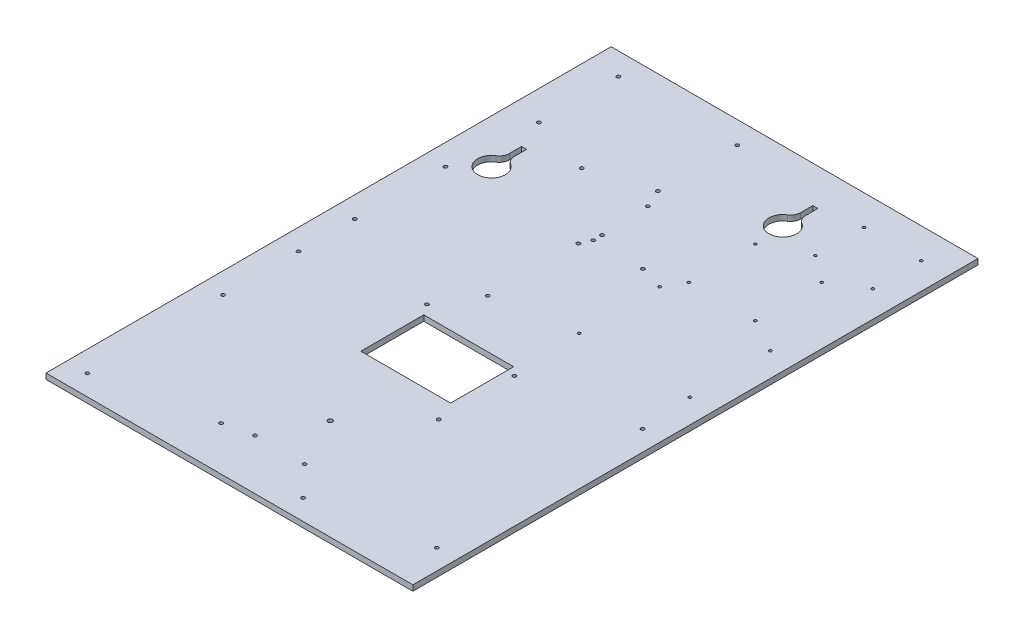
SolidWorks part; units mm, degrees
material "Acrylic (Medium-high impact)"
ref_plane "Front Plane" through (0, 0, 0) normal (0, 0, 1) x (1, 0, 0)
ref_plane "Top Plane" through (0, 0, 0) normal (0, 1, 0) x (1, 0, 0)
ref_plane "Right Plane" through (0, 0, 0) normal (1, 0, 0) x (0, 0, -1)
sketch "Sketch1" plane through (0, 0, 0) normal (0, 1, 0) x (1, 0, 0)
  line L0 (-836.7628, 790.2433) -> (-836.7628, 232.9433)
  line L1 (-836.7628, 790.2433) -> (-836.7628, 796.5933)
  line L2 (-836.7628, 796.5933) -> (-466.7628, 796.5933)
  line L3 (-466.7628, 796.5933) -> (-466.7628, 790.2433)
  line L4 (-836.7628, 232.9433) -> (-836.7628, 226.5933)
  line L5 (-836.7628, 226.5933) -> (-466.7628, 226.5933)
  line L6 (-466.7628, 226.5933) -> (-466.7628, 232.9433)
  line L7 (-466.7628, 790.2433) -> (-836.7628, 790.2433) construction
  line L8 (-466.7628, 232.9433) -> (-466.7628, 790.2433)
  line L9 (-836.7628, 232.9433) -> (-466.7628, 232.9433) construction
  circle A0 centre (-807.0628, 774.0873) radius 1.778
  circle A1 centre (-807.0628, 694.0873) radius 1.778
  circle A2 centre (-687.0628, 694.0873) radius 1.778
  circle A3 centre (-687.0628, 774.0873) radius 1.778
  circle A4 centre (-551.4378, 766.1683) radius 1.397
  circle A5 centre (-551.4378, 717.1683) radius 1.397
  circle A6 centre (-493.4378, 717.1683) radius 1.397
  circle A7 centre (-493.4378, 766.1683) radius 1.397
  circle A8 centre (-591.7378, 696.9683) radius 1.397
  circle A9 centre (-591.7378, 629.9683) radius 1.397
  circle A10 centre (-524.7378, 629.9683) radius 1.397
  circle A11 centre (-524.7378, 696.9683) radius 1.397
  circle A12 centre (-815.5538, 608.2133) radius 1.778
  circle A13 centre (-681.4418, 608.2133) radius 1.778
  circle A14 centre (-681.4418, 516.7733) radius 1.778
  circle A15 centre (-815.5538, 516.7733) radius 1.778
  circle A16 centre (-602.6528, 611.4033) radius 1.397
  circle A17 centre (-602.6528, 530.1233) radius 1.397
  circle A18 centre (-490.8928, 611.4033) radius 1.397
  circle A19 centre (-490.8928, 530.1233) radius 1.397
  circle A20 centre (-487.0828, 478.6733) radius 1.778
  circle A21 centre (-598.0808, 460.2583) radius 1.778
  circle A22 centre (-598.0808, 384.0583) radius 1.778
  circle A23 centre (-487.0828, 271.0918) radius 1.778
  circle A24 centre (-598.0808, 247.1523) radius 1.778
  circle A25 centre (-704.6828, 271.0918) radius 1.778
  circle A26 centre (-815.6808, 247.1523) radius 1.778
  circle A27 centre (-815.6808, 384.0583) radius 1.778
  circle A28 centre (-815.6808, 460.2583) radius 1.778
  circle A29 centre (-704.6828, 478.6733) radius 1.778
  circle A30 centre (-678.9408, 675.7392) radius 1.778
  circle A31 centre (-745.5396, 675.7392) radius 1.778
  circle A32 centre (-676.7908, 627.4952) radius 1.778
  dimension "D1" = 2.794
  dimension "D2" = 3.556
  dimension "D10" = 3.556
  dimension "D11" = 120.8541
  dimension "D13" = 3.556
  dimension "D14" = 3.556
  dimension "D3" = 232.9433
  dimension "D4" = 790.2433
  dimension "D5" = 370
  dimension "D6" = 370
  dimension "D7" = 466.7628
  dimension "D8" = 466.7628
  dimension "D9" = 557.3
  dimension "D12" = 157.822
  dimension "D15" = 66.5988
  dimension "D16" = 2.15
  dimension "D17" = 48.244
extrude "Boss-Extrude1" add sketch "Sketch1" along normal blind 5.6388
sketch "Sketch5" plane through (0, 0, 0) normal (0, -1, 0) x (1, 0, 0)
  line L0 (-794.8528, -664.2805) -> (-794.8528, -651.9215)
  line L1 (-794.8528, -631.4933) -> (-789.7728, -631.4933) construction
  line L2 (-794.8528, -631.4933) -> (-794.8528, -664.2805) construction
  line L3 (-794.8528, -664.2805) -> (-789.7728, -664.2805)
  line L4 (-789.7728, -631.4933) -> (-789.7728, -664.2805) construction
  line L5 (-596.3028, -759.5305) -> (-596.3028, -747.1715)
  line L6 (-596.3028, -726.7433) -> (-591.2228, -726.7433) construction
  line L7 (-596.3028, -726.7433) -> (-596.3028, -759.5305) construction
  line L8 (-596.3028, -759.5305) -> (-591.2228, -759.5305)
  line L9 (-789.7728, -664.2805) -> (-789.7728, -651.9215)
  line L10 (-591.2228, -726.7433) -> (-591.2228, -759.5305) construction
  line L11 (-591.2228, -759.5305) -> (-591.2228, -747.1715)
  line L12 (-836.7628, -796.5933) -> (-836.7628, -226.5933) construction
  line L14 (-466.7628, -226.5933) -> (-466.7628, -796.5933) construction
  line L15 (-466.7628, -796.5933) -> (-836.7628, -796.5933) construction
  line L16 (-836.7628, -226.5933) -> (-466.7628, -226.5933) construction
  line L17 (-466.7628, -226.5933) -> (-466.7628, -796.5933) construction
  arc A0 (-785.0043, -643.3991) -> (-799.6213, -643.3991) centre (-792.3128, -631.4933) ccw
  arc A1 (-586.4543, -738.6491) -> (-601.0713, -738.6491) centre (-593.7628, -726.7433) ccw
  arc A2 (-789.7728, -651.9215) -> (-785.0043, -643.3991) centre (-779.7728, -651.9215) cw
  arc A3 (-794.8528, -651.9215) -> (-799.6213, -643.3991) centre (-804.8528, -651.9215) ccw
  arc A4 (-591.2228, -747.1715) -> (-586.4543, -738.6491) centre (-581.2228, -747.1715) cw
  arc A5 (-596.3028, -747.1715) -> (-601.0713, -738.6491) centre (-606.3028, -747.1715) ccw
  circle A6 centre (-651.7628, -328.1933) radius 2.394
  point P15 (-789.7728, -645.2305)
  point P18 (-794.8528, -645.2305)
  dimension "D1" = 27.94
  dimension "D3" = 10
  dimension "D4" = 27.94
  dimension "D5" = 10
  dimension "D7" = 165.1
  dimension "D13" = 4.7879
  dimension "D2" = 19.05
  dimension "D6" = 44.45
  dimension "D8" = 32.7872
  dimension "D9" = 32.7872
  dimension "D10" = 69.85
  dimension "D11" = 127
  dimension "D12" = 12.359
  dimension "D14" = 101.6
  dimension "D15" = 185
extrude "Cut-Extrude1" cut sketch "Sketch5" against normal through all
sketch "Sketch6" plane through (0, 5.6388, 0) normal (0, 1, 0) x (1, 0, 0)
  line L0 (-836.7628, 226.5933) -> (-466.7628, 226.5933) construction
  line L1 (-836.7628, 796.5933) -> (-836.7628, 226.5933) construction
  line L2 (-466.7628, 226.5933) -> (-466.7628, 796.5933) construction
  line L3 (-466.7628, 796.5933) -> (-836.7628, 796.5933) construction
  circle A0 centre (-676.7628, 277.3933) radius 1.778
  circle A1 centre (-626.7628, 277.3933) radius 1.778
  circle A2 centre (-676.7628, 618.5933) radius 1.778
  circle A3 centre (-626.7628, 618.5933) radius 1.778
  dimension "D1" = 3.556
  dimension "D2" = 3.556
  dimension "D6" = 3.556
  dimension "D7" = 3.556
  dimension "D3" = 50.8
  dimension "D4" = 160
  dimension "D5" = 160
  dimension "D8" = 160
  dimension "D9" = 160
  dimension "D10" = 178
extrude "Cut-Extrude2" cut sketch "Sketch6" against normal through all
sketch "Sketch7" plane through (0, 5.6388, 0) normal (0, 1, 0) x (1, 0, 0)
  line L0 (-836.7628, 226.5933) -> (-466.7628, 226.5933) construction
  line L1 (-606.4628, 467.8933) -> (-697.0628, 467.8933)
  line L2 (-606.4628, 467.8933) -> (-606.4628, 404.3933)
  line L3 (-606.4628, 404.3933) -> (-697.0628, 404.3933)
  line L4 (-697.0628, 467.8933) -> (-697.0628, 404.3933)
  line L5 (-606.4628, 467.8933) -> (-697.0628, 404.3933) construction
  line L6 (-606.4628, 404.3933) -> (-697.0628, 467.8933) construction
  line L7 (-466.7628, 226.5933) -> (-466.7628, 796.5933) construction
  line L8 (-836.7628, 796.5933) -> (-836.7628, 226.5933) construction
  point P0 (-651.7628, 436.1433)
  dimension "D1" = 177.8
  dimension "D2" = 139.7
  dimension "D3" = 139.7
  dimension "D4" = 63.5
extrude "Cut-Extrude3" cut sketch "Sketch7" against normal through all
